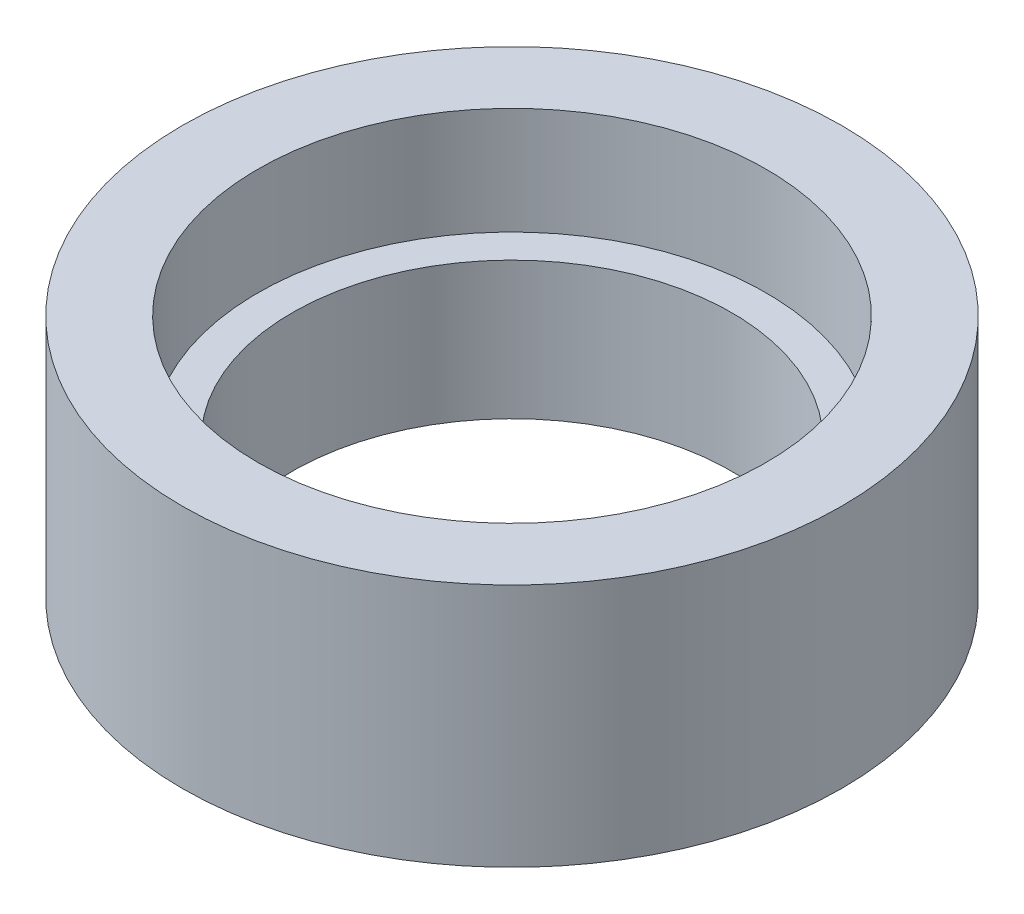
SolidWorks part; units mm, degrees
ref_plane "前视基准面" through (0, 0, 0) normal (0, 0, 1) x (1, 0, 0)
ref_plane "上视基准面" through (0, 0, 0) normal (0, 1, 0) x (1, 0, 0)
ref_plane "右视基准面" through (0, 0, 0) normal (1, 0, 0) x (0, 0, -1)
other "Configuration Table"
sketch "草图1" plane through (0, 0, 0) normal (0, 1, 0) x (1, 0, 0)
  circle A0 centre (0, 0) radius 8
  circle A1 centre (0, 0) radius 12
  dimension "D1" = 16
  dimension "D2" = 24
extrude "凸台-拉伸1" add sketch "草图1" along normal blind 5
sketch "草图3" plane through (0, 5, 0) normal (0, 1, 0) x (1, 0, 0)
  circle A0 centre (0, 0) radius 9.25
  circle A1 centre (0, 0) radius 12
  dimension "D1" = 18.5
  dimension "D2" = 24
extrude "凸台-拉伸2" add sketch "草图3" along normal blind 3.9
